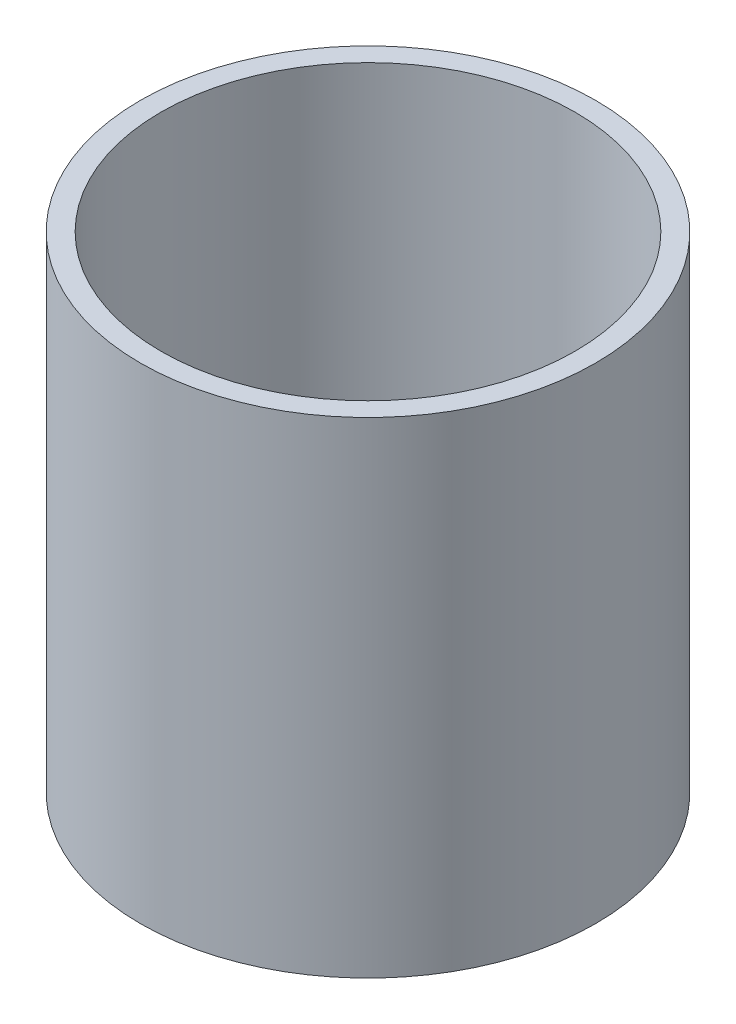
SolidWorks part; units mm, degrees
material "ABS PLASTIC"
ref_plane "Front Plane" through (0, 0, 0) normal (0, 0, 1) x (1, 0, 0)
ref_plane "Top Plane" through (0, 0, 0) normal (0, 1, 0) x (1, 0, 0)
ref_plane "Right Plane" through (0, 0, 0) normal (1, 0, 0) x (0, 0, -1)
sketch "Sketch1" plane through (0, 0, 0) normal (0, 1, 0) x (1, 0, 0)
  circle A0 centre (0, 0) radius 19.05
  circle A1 centre (0, 0) radius 17.3355
  dimension "D1" = 38.1
  dimension "D2" = 34.671
extrude "Boss-Extrude1" add sketch "Sketch1" along normal blind 40.64
